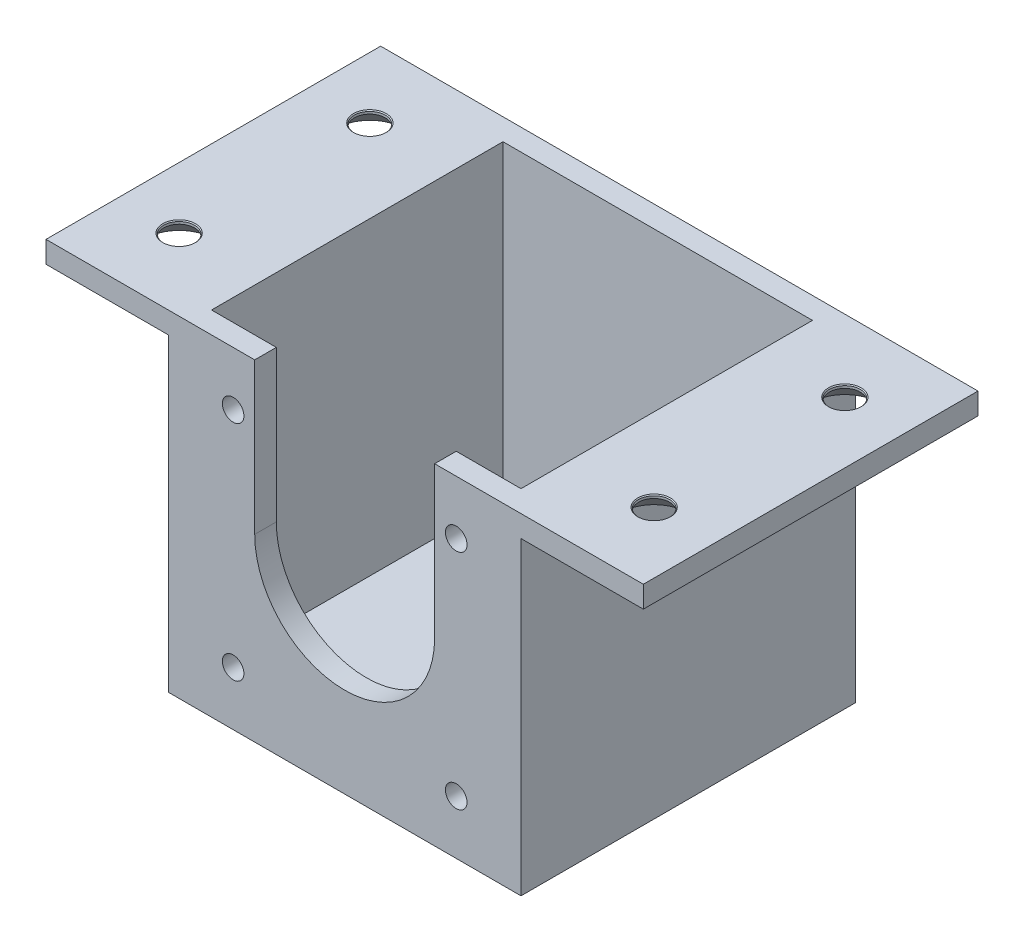
SolidWorks part; units mm, degrees
material "Alliage 1060"
ref_plane "Plan de dessus" through (0, 0, 0) normal (0, 0, 1) x (1, 0, 0)
ref_plane "Plan de droite" through (0, 0, 0) normal (0, 1, 0) x (1, 0, 0)
ref_plane "Plan de face" through (0, 0, 0) normal (1, 0, 0) x (0, 0, -1)
sketch "Esquisse1" plane through (0, 0, 0) normal (0, 0, 1) x (1, 0, 0)
  line L0 (0, 0) -> (-43, 0)
  line L1 (-43, 0) -> (-43, 43)
  line L2 (-43, 43) -> (-63, 43)
  line L3 (0, 0) -> (0, 43)
  line L4 (0, 43) -> (20, 43)
  dimension "D1" = 43
  dimension "D2" = 43
  dimension "D3" = 20
extrude "Extru.-Mince1" add sketch "Esquisse1" along normal blind 46.5 thin thin type one direction wall 3
sketch "Esquisse2" plane through (0, 0, 0) normal (0, 1, 0) x (1, 0, 0)
  line L0 (-43, -46.5) -> (-43, 0) construction
  line L1 (-43, -3) -> (0, -3)
  line L2 (-43, -3) -> (-43, 0)
  line L3 (-43, 0) -> (0, 0)
  line L4 (0, -3) -> (0, 0)
  line L5 (-43, -23.25) -> (0, -23.25) construction
  line L6 (0, -46.5) -> (0, 0) construction
  line L7 (0, -43.5) -> (0, -46.5)
  line L8 (-43, -46.5) -> (0, -46.5)
  line L9 (-43, -43.5) -> (-43, -46.5)
  line L10 (-43, -43.5) -> (0, -43.5)
  dimension "D1" = 3
extrude "Boss.-Extru.1" add sketch "Esquisse2" along normal up to vertex (43 mm away) up to point (-43, 43, 0)
sketch "Esquisse3" plane through (0, 0, 46.5) normal (0, 0, 1) x (1, 0, 0)
  line L0 (-63, 43) -> (20, 43) construction
  line L1 (-34, 43) -> (-9, 43)
  line L2 (-34, 43) -> (-34, 22)
  line L3 (-34, 22) -> (-9, 22) construction
  line L4 (-9, 43) -> (-9, 22)
  line L5 (-46, -3) -> (3, -3) construction
  line L6 (-6, 4.5) -> (-37, 4.5) construction
  line L7 (-6, 4.5) -> (-6, 35.5) construction
  line L8 (-6, 35.5) -> (-37, 35.5) construction
  line L9 (-37, 4.5) -> (-37, 35.5) construction
  line L10 (-6, 4.5) -> (-37, 35.5) construction
  line L11 (-6, 35.5) -> (-37, 4.5) construction
  line L12 (3, -3) -> (3, 43) construction
  arc A0 (-9, 22) -> (-34, 22) centre (-21.5, 22) cw
  circle A1 centre (-21.5, 20) radius 21.9203 construction
  circle A3 centre (-37, 4.5) radius 1.5
  circle A4 centre (-37, 35.5) radius 1.5
  circle A5 centre (-6, 35.5) radius 1.5
  circle A6 centre (-6, 4.5) radius 1.5
  point P8 (-21.5, 43)
  point P13 (-21.5, 20)
  point P17 (-21.5, -3)
  point P21 (3, 20)
  dimension "D2" = 12.5
  dimension "D4" = 3
  dimension "D5" = 3
  dimension "D6" = 3
  dimension "D7" = 3
  dimension "D1" = 21
  dimension "D3" = 31
extrude "Enlèv. mat.-Extru.1" cut sketch "Esquisse3" against normal up to next
hole_wizard "Fraisage pour vis à tête fraisée M41" positions "Esquisse4" profile "Esquisse5" countersink size "M4" standard "ISO" end condition through all
sketch "Esquisse4" plane through (0, 40, 0) normal (0, -1, 0) x (-1, 0, 0)
  line L0 (-11.5, 0) -> (-11.5, -46.5) construction
  line L1 (-3, 0) -> (-20, 0) construction
  line L2 (-3, -46.5) -> (-20, -46.5) construction
  line L11 (-3, -46.5) -> (46, -46.5) construction
  line L14 (21.5, -46.5) -> (21.5, -33.3942) construction
  point P24 (-11.5, -10)
  point P26 (-11.5, -36.5)
  point P54 (54.5, -10)
  point P55 (54.5, -36.5)
  dimension "D1" = 10
  dimension "D2" = 10
sketch "Esquisse5" plane through (-54.5, 40, 36.5) normal (1, 0, 0) x (0, 0, -1)
  line L0 (0, 0) -> (0, 3)
  line L1 (0, 3) -> (2.275, 3)
  line L2 (2.15, 2.875) -> (2.15, 2.55)
  line L3 (2.15, 2.55) -> (4.7, 0)
  line L5 (4.7, 0) -> (0, 0)
  line L6 (-2.15, 2.55) -> (-4.7, 0) construction
  line L7 (2.275, 3) -> (2.15, 2.875)
  line L8 (-2.275, 3) -> (-2.15, 2.875) construction
  line L11 (0, -6.35) -> (0, 107.95) construction
  dimension "Diamètre du perçage jusqu'au prochain" = 4.3
  dimension "Profondeur du perçage jusqu'au prochain" = 3
  dimension "Diamètre du fraisage entrant" = 9.4
  dimension "Angle du fraisage entrant" = 90
  dimension "Diamètre du fraisage débouchant" = 4.55
  dimension "Angle du fraisage débouchant" = 90
sketch "Esquisse6" plane through (0, -3, 0) normal (0, -1, 0) x (1, 0, 0)
  line L0 (-46, 0) -> (3, 0) construction
  line L1 (-9, 0) -> (-34, 0)
  line L2 (-9, 0) -> (-9, 15)
  line L3 (-9, 15) -> (-34, 15)
  line L4 (-34, 0) -> (-34, 15)
  point P6 (-21.5, 15)
  point P7 (-21.5, 0)
  dimension "D1" = 15
  dimension "D2" = 25
extrude "Enlèv. mat.-Extru.2" cut sketch "Esquisse6" against normal blind 5
